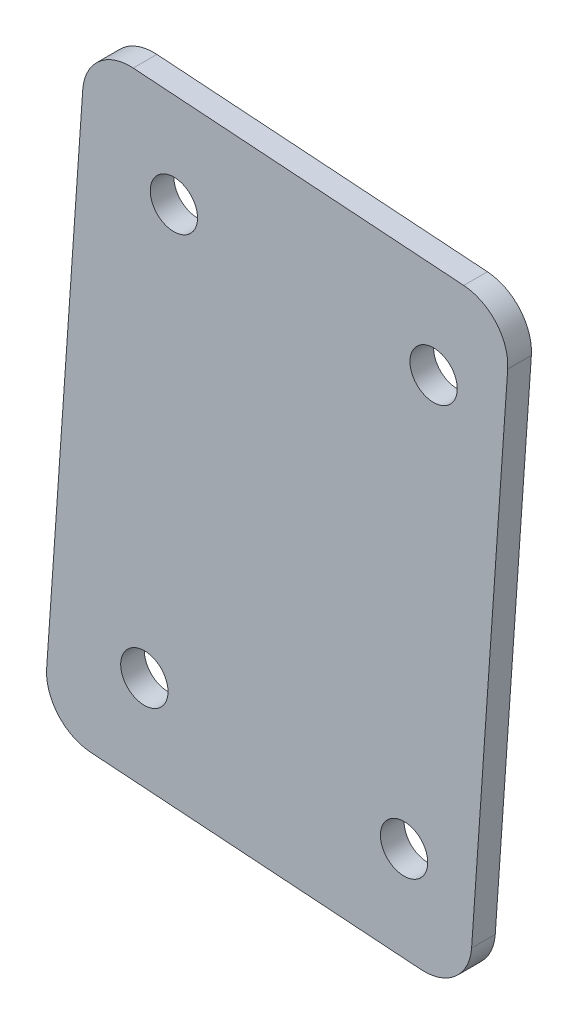
SolidWorks part; units mm, degrees
material "6061-T6 (SS)"
ref_plane "Front Plane" through (0, 0, 0) normal (0, 0, 1) x (1, 0, 0)
ref_plane "Top Plane" through (0, 0, 0) normal (0, 1, 0) x (1, 0, 0)
ref_plane "Right Plane" through (0, 0, 0) normal (1, 0, 0) x (0, 0, -1)
sketch "Sketch1" plane through (0, 0, 0) normal (0, 0, 1) x (1, 0, 0)
  line L0 (-341.6123, 331.6918) -> (-306.7713, 329.2709) construction
  line L1 (-306.7713, 329.2709) -> (-310.7327, 272.2584) construction
  line L2 (-345.5737, 274.6793) -> (-310.7327, 272.2584) construction
  line L3 (-353.4014, 345.2416) -> (-296.3889, 341.2801)
  line L4 (-353.4014, 345.2416) -> (-359.1235, 262.8901)
  line L5 (-359.1235, 262.8901) -> (-302.111, 258.9287)
  line L6 (-296.3889, 341.2801) -> (-302.111, 258.9287)
  circle A0 centre (-306.7713, 329.2709) radius 3.175 construction
  circle A1 centre (-341.6123, 331.6918) radius 3.175 construction
  circle A2 centre (-345.5737, 274.6793) radius 3.175 construction
  circle A3 centre (-310.7327, 272.2584) radius 3.175 construction
  circle A4 centre (-306.7713, 329.2709) radius 3.175
  circle A5 centre (-341.6123, 331.6918) radius 3.175
  circle A6 centre (-345.5737, 274.6793) radius 3.175
  circle A7 centre (-310.7327, 272.2584) radius 3.175
  dimension "D1" = 9.525
  dimension "D2" = 12.7
  dimension "D3" = 12.7
  dimension "D4" = 12.7
extrude "Boss-Extrude1" add sketch "Sketch1" along normal blind 3.175
fillet "Fillet1" radius 6.35 4 edges at (-296.3889, 341.2801, 1.5875) (-302.111, 258.9287, 1.5875) (-359.1235, 262.8901, 1.5875) (-353.4014, 345.2416, 1.5875)
